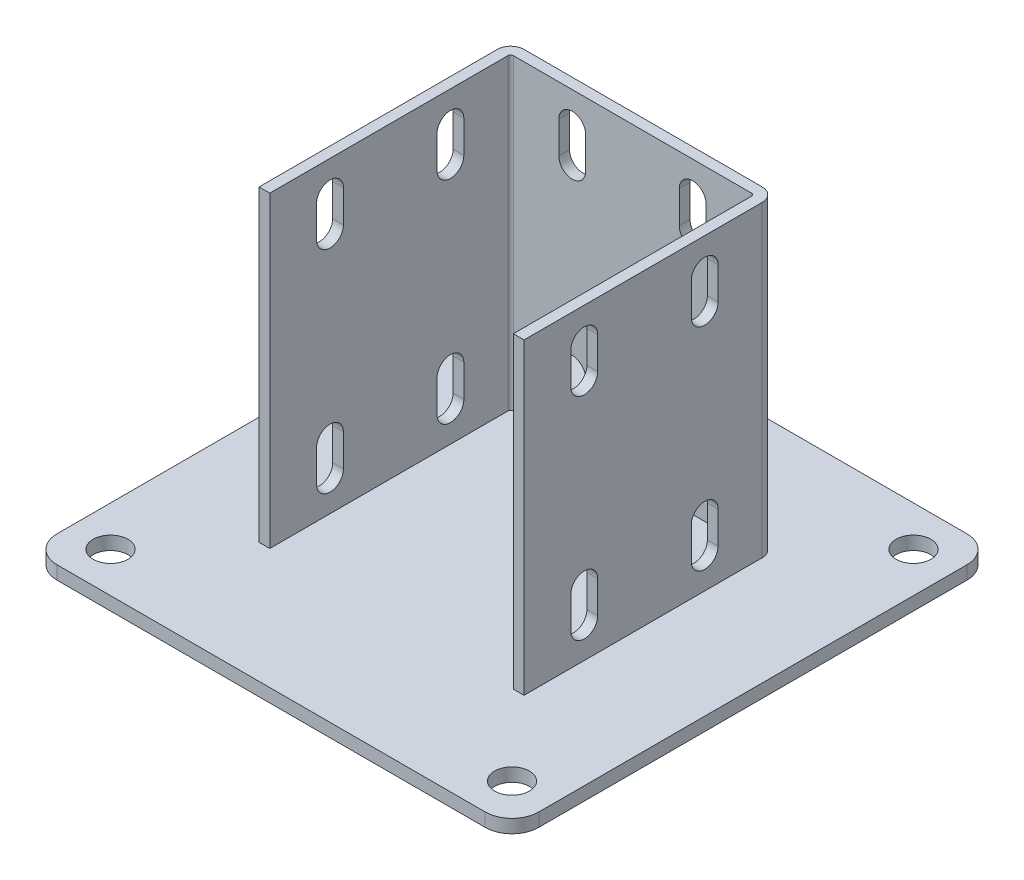
SolidWorks part; units mm, degrees
material "Ст3пс ГОСТ 380-2005"
ref_plane "Спереди" through (0, 0, 0) normal (0, 0, 1) x (1, 0, 0)
ref_plane "Сверху" through (0, 0, 0) normal (0, 1, 0) x (1, 0, 0)
ref_plane "Справа" through (0, 0, 0) normal (1, 0, 0) x (0, 0, -1)
sketch "Эскиз2" plane through (0, 0, 0) normal (0, 1, 0) x (1, 0, 0)
  line L1 (-90, -90) -> (90, -90)
  line L2 (-90, -90) -> (-90, 90)
  line L3 (-90, 90) -> (90, 90)
  line L4 (90, -90) -> (90, 90)
  line L5 (-90, -90) -> (90, 90) construction
  line L6 (-90, 90) -> (90, -90) construction
  point P0 (0, 0)
  dimension "D2" = 180
extrude "Бобышка-Вытянуть1" add sketch "Эскиз2" along normal blind 5
sketch "Эскиз3" plane through (0, 5, 0) normal (0, 1, 0) x (1, 0, 0)
  line L0 (-45.5, -45) -> (-45.5, 45)
  line L1 (-45.5, 45) -> (45.5, 45)
  line L2 (45.5, 45) -> (45.5, -45)
  point P2 (0, 45)
  point P5 (-45.5, 0)
  dimension "D2" = 91
  dimension "D3" = 90
extrude "Вытянуть-Тонкостенный1" add sketch "Эскиз3" along normal offset from surface (115 mm away) 120 thin up to face at (0, 0, 0) thin type one direction reverse wall 4
sketch "Эскиз4" plane through (0, 0, 0) normal (1, 0, 0) x (0, 0, -1)
  line L0 (49, 67.3538) -> (85, 5)
  line L1 (49, 120) -> (49, 5) construction
  line L2 (-90, 5) -> (90, 5) construction
  line L3 (85, 5) -> (49, 5)
  line L4 (49, 5) -> (49, 67.3538)
  line L5 (90, 5) -> (90, 0) construction
  dimension "D1" = 30
  dimension "D2" = 5
extrude "Бобышка-Вытянуть2" add sketch "Эскиз4" along normal mid plane 4
sketch "Эскиз5" plane through (49.5, 0, 0) normal (1, 0, 0) x (0, 0, -1)
  line L0 (-22.5, 108) -> (-22.5, 96) construction
  line L1 (-17.5, 108) -> (-17.5, 96)
  line L2 (-27.5, 108) -> (-27.5, 96)
  line L3 (-22.5, 29) -> (-22.5, 17) construction
  line L4 (-17.5, 29) -> (-17.5, 17)
  line L5 (-27.5, 29) -> (-27.5, 17)
  line L6 (-45, 120) -> (44, 120) construction
  line L7 (-90, 5) -> (90, 5) construction
  line L8 (0, 0) -> (0, 63.8564) construction
  line L11 (22.5, 108) -> (22.5, 96) construction
  line L14 (17.5, 108) -> (17.5, 96)
  line L15 (27.5, 108) -> (27.5, 96)
  line L16 (22.5, 29) -> (22.5, 17) construction
  line L17 (17.5, 29) -> (17.5, 17)
  line L18 (27.5, 29) -> (27.5, 17)
  arc A0 (-17.5, 108) -> (-27.5, 108) centre (-22.5, 108) ccw
  arc A1 (-27.5, 96) -> (-17.5, 96) centre (-22.5, 96) ccw
  arc A2 (-17.5, 29) -> (-27.5, 29) centre (-22.5, 29) ccw
  arc A3 (-27.5, 17) -> (-17.5, 17) centre (-22.5, 17) ccw
  arc A8 (17.5, 108) -> (27.5, 108) centre (22.5, 108) cw
  arc A9 (27.5, 96) -> (17.5, 96) centre (22.5, 96) cw
  arc A10 (17.5, 29) -> (27.5, 29) centre (22.5, 29) cw
  arc A11 (27.5, 17) -> (17.5, 17) centre (22.5, 17) cw
  point P3 (-22.5, 102)
  point P8 (-22.5, 23)
  point P22 (22.5, 102)
  point P29 (22.5, 23)
extrude "Вырез-Вытянуть1" cut sketch "Эскиз5" against normal through all
sketch "Эскиз6" plane through (0, 5, 0) normal (0, 1, 0) x (1, 0, 0)
  line L0 (-90, 90) -> (-90, -90) construction
  line L1 (75, -75) -> (-75, -75) construction
  line L2 (75, -75) -> (75, 75) construction
  line L3 (75, 75) -> (-75, 75) construction
  line L4 (-75, -75) -> (-75, 75) construction
  line L5 (75, -75) -> (-75, 75) construction
  line L6 (75, 75) -> (-75, -75) construction
  line L7 (90, 90) -> (-90, 90) construction
  circle A0 centre (-75, 75) radius 6.5
  circle A1 centre (-75, -75) radius 6.5
  circle A2 centre (75, 75) radius 6.5
  circle A3 centre (75, -75) radius 6.5
  point P0 (0, 0)
  dimension "D1" = 13
  dimension "D2" = 15
  dimension "D3" = 15
extrude "Вырез-Вытянуть2" cut sketch "Эскиз6" against normal through all
fillet "Скругление1" radius 10 4 edges at (90, 2.5, 90) (-90, 2.5, 90) (-90, 2.5, -90) (90, 2.5, -90)
sketch "Эскиз8" plane through (0, 0, -49) normal (0, 0, -1) x (-1, 0, 0)
  line L0 (-22.5, 108) -> (-22.5, 96) construction
  line L1 (-17.5, 108) -> (-17.5, 96)
  line L2 (-27.5, 108) -> (-27.5, 96)
  line L3 (-22.5, 29) -> (-22.5, 17) construction
  line L4 (-17.5, 29) -> (-17.5, 17)
  line L5 (-27.5, 29) -> (-27.5, 17)
  line L6 (-44.5, 120) -> (44.5, 120) construction
  line L7 (-80, 5) -> (80, 5) construction
  line L8 (0, 0) -> (0, 80) construction
  line L9 (-80, 0) -> (80, 0) construction
  line L10 (22.5, 108) -> (22.5, 96) construction
  line L11 (17.5, 108) -> (17.5, 96)
  line L12 (27.5, 108) -> (27.5, 96)
  line L13 (22.5, 29) -> (22.5, 17) construction
  line L14 (17.5, 29) -> (17.5, 17)
  line L15 (27.5, 29) -> (27.5, 17)
  arc A0 (-17.5, 108) -> (-27.5, 108) centre (-22.5, 108) ccw
  arc A1 (-27.5, 96) -> (-17.5, 96) centre (-22.5, 96) ccw
  arc A2 (-17.5, 29) -> (-27.5, 29) centre (-22.5, 29) ccw
  arc A3 (-27.5, 17) -> (-17.5, 17) centre (-22.5, 17) ccw
  arc A4 (17.5, 108) -> (27.5, 108) centre (22.5, 108) cw
  arc A5 (27.5, 96) -> (17.5, 96) centre (22.5, 96) cw
  arc A6 (17.5, 29) -> (27.5, 29) centre (22.5, 29) cw
  arc A7 (27.5, 17) -> (17.5, 17) centre (22.5, 17) cw
  point P2 (-22.5, 102)
  point P7 (-22.5, 23)
  point P24 (22.5, 102)
  point P31 (22.5, 23)
extrude "Вырез-Вытянуть3" cut sketch "Эскиз8" against normal up to next
equation "\"D5@Эскиз5\"=\"D5@Эскиз8\""
